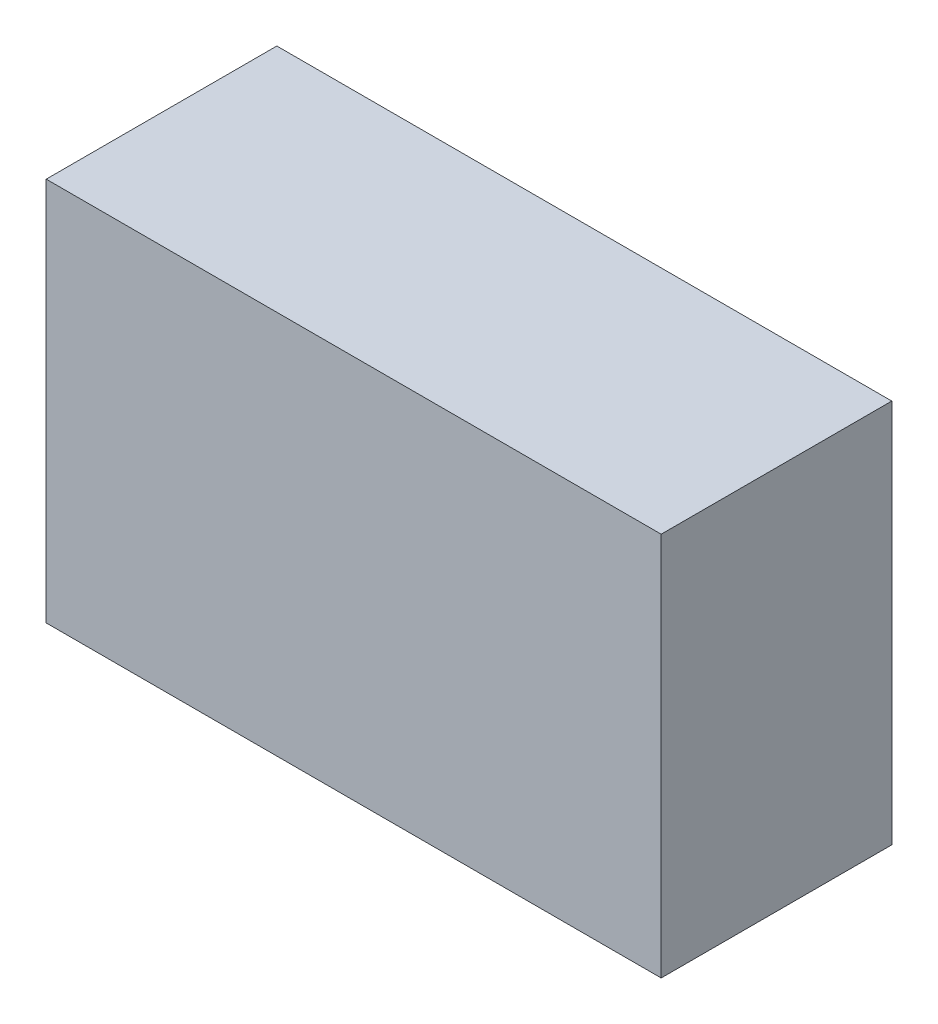
SolidWorks part; units mm, degrees
ref_plane "Front Plane" through (0, 0, 0) normal (0, 0, 1) x (1, 0, 0)
ref_plane "Top Plane" through (0, 0, 0) normal (0, 1, 0) x (1, 0, 0)
ref_plane "Right Plane" through (0, 0, 0) normal (1, 0, 0) x (0, 0, -1)
sketch "Sketch1" plane through (0, 0, 0) normal (0, 0, 1) x (1, 0, 0)
  line L0 (0, -300) -> (-10900, -300) construction
  line L1 (-9050, -300) -> (-5050, -300)
  line L2 (-9050, -300) -> (-9050, -2800)
  line L3 (-9050, -2800) -> (-5050, -2800)
  line L4 (-5050, -300) -> (-5050, -2800)
  line L5 (-11050, -56390) -> (-11050, 0) construction
  dimension "D1" = 2500
  dimension "D2" = 2000
  dimension "D3" = 4000
extrude "Extrude1" add sketch "Sketch1" along normal blind 1500
